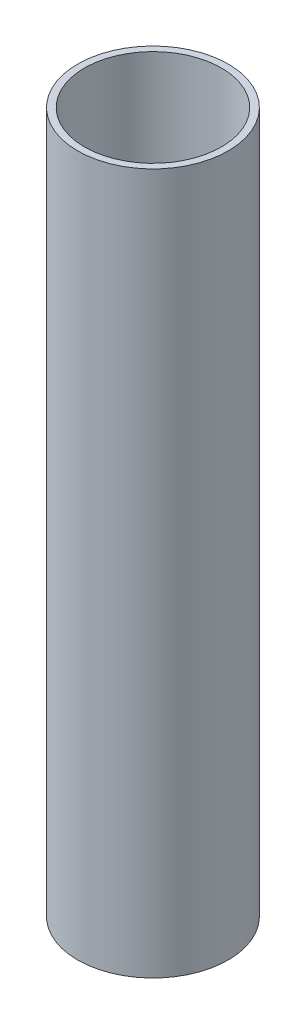
SolidWorks part; units mm, degrees
material "Corrugated Paper"
ref_plane "Front Plane" through (0, 0, 0) normal (0, 0, 1) x (1, 0, 0)
ref_plane "Top Plane" through (0, 0, 0) normal (0, 1, 0) x (1, 0, 0)
ref_plane "Right Plane" through (0, 0, 0) normal (1, 0, 0) x (0, 0, -1)
sketch "Sketch1" plane through (0, 0, 0) normal (0, 1, 0) x (1, 0, 0)
  circle A0 centre (0, 0) radius 38.1
  circle A1 centre (0, 0) radius 41.9
  dimension "D1" = 83.8
  dimension "D2" = 76.2
extrude "Boss-Extrude1" add sketch "Sketch1" along normal blind 390
